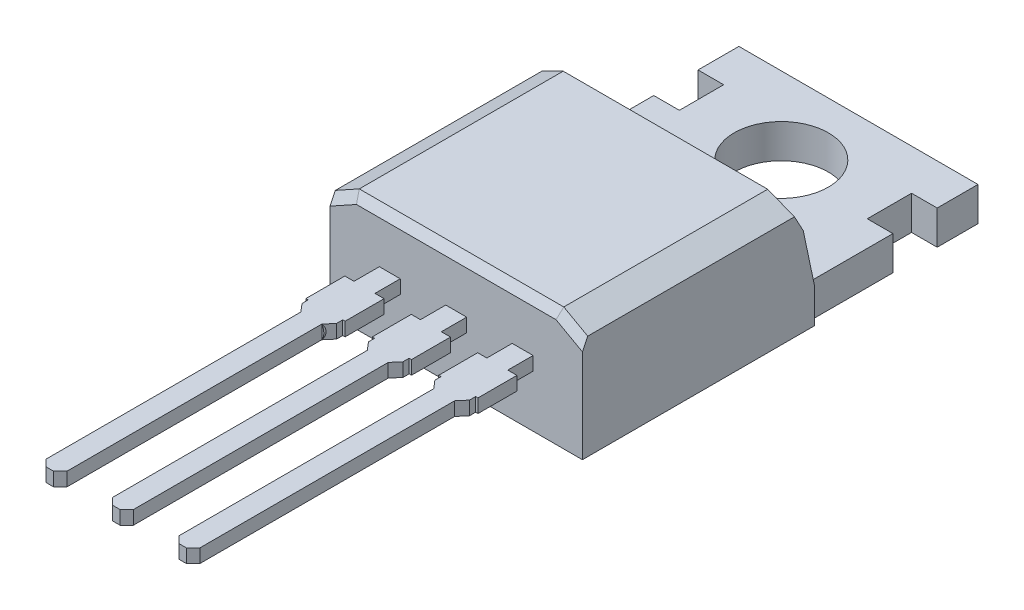
SolidWorks part; units mm, degrees
ref_plane "Front Plane" through (0, 0, 0) normal (0, 0, 1) x (1, 0, 0)
ref_plane "Top Plane" through (0, 0, 0) normal (0, 1, 0) x (1, 0, 0)
ref_plane "Right Plane" through (0, 0, 0) normal (1, 0, 0) x (0, 0, -1)
sketch "Sketch1" plane through (0, 0, 0) normal (0, 1, 0) x (1, 0, 0)
  line L0 (4.826, -1.0795) -> (-4.826, -1.0795)
  line L1 (4.826, -7.3025) -> (-4.826, -7.3025)
  line L2 (4.826, -7.3025) -> (4.826, 8.2138)
  line L3 (4.826, 7.3025) -> (-4.826, 7.3025)
  line L4 (-4.826, -7.3025) -> (-4.826, 8.2138)
  line L5 (4.826, -7.3025) -> (-4.826, 7.3025) construction
  line L6 (4.826, 7.3025) -> (-4.826, -7.3025) construction
  line L7 (4.826, -1.0795) -> (-4.826, -1.0795)
  line L8 (3.7898, 8.9789) -> (-3.7898, 8.9789)
  line L9 (-4.826, 8.2138) -> (-3.7898, 8.9789)
  line L10 (0, 7.3025) -> (0, 12.7866) construction
  line L11 (4.826, 8.2138) -> (3.7898, 8.9789)
  line L12 (4.826, 8.9789) -> (-4.826, 8.9789) construction
  point P0 (0, 0)
  dimension "D1" = 9.652
  dimension "D2" = 14.605
  dimension "D3" = 8.382
  dimension "D4" = 8.382
  dimension "D5" = 1.6764
sketch "Sketch2" plane through (0, 0, 0) normal (1, 0, 0) x (0, 0, -1)
  line L0 (14.3005, 0) -> (-1.0795, 0)
  line L1 (7.3025, 0) -> (12.7866, 0) construction
  line L2 (7.8005, 1.3) -> (7.124, 4.5)
  line L3 (7.124, 4.5) -> (-1.0795, 4.5)
  line L4 (-1.0795, 4.5) -> (-1.0795, 0)
  line L5 (14.3005, 1.3) -> (14.3005, 0)
  line L6 (14.3005, 1.3) -> (7.8005, 1.3)
  line L7 (14.3005, 1.3) -> (-7.3025, 1.3) construction
  line L8 (14.3005, 0) -> (-7.3025, 0) construction
  dimension "D1" = 4.5
  dimension "D3" = 6.5
  dimension "D2" = 15.38
extrude "Extrude1" add sketch "Sketch2" against normal up to vertex (4.826 mm away) and the other way up to vertex (4.826 mm away) up to point (-4.826, 0, 1.0795) other way up to point (4.826, 0, 1.0795)
sketch "Sketch10" plane through (0, 1.3, 0) normal (0, 1, 0) x (1, 0, 0)
  line L0 (0, 7.8005) -> (0, 16.6747) construction
  line L1 (-4.826, 7.8005) -> (4.826, 7.8005) construction
  line L2 (-4.826, 14.3005) -> (4.826, 14.3005) construction
  line L3 (-4.826, 14.3005) -> (-4.826, 7.8005) construction
  line L4 (-4.826, 12.7393) -> (-3.5922, 12.7393)
  line L5 (-4.826, 12.7393) -> (-4.826, 11.0462)
  line L6 (-4.826, 11.0462) -> (-3.5922, 11.0462)
  line L7 (-3.5922, 12.7393) -> (-3.5922, 11.0462)
  line L8 (3.5922, 12.7393) -> (3.5922, 11.0462)
  line L9 (4.826, 11.0462) -> (3.5922, 11.0462)
  line L10 (4.826, 12.7393) -> (4.826, 11.0462)
  line L11 (4.826, 12.7393) -> (3.5922, 12.7393)
  circle A0 centre (0, 11.3505) radius 1.8
  dimension "D1" = 3.6
  dimension "D2" = 2.95
extrude "Extrude5" cut sketch "Sketch10" against normal through all
sketch "Sketch6" plane through (0, 0, 1.0795) normal (0, 0, 1) x (1, 0, 0)
  line L0 (0, 4.5) -> (0, 0) construction
  line L1 (-4.826, 4.5) -> (4.826, 4.5) construction
  line L2 (-2.54, 4.5) -> (-2.54, 0) construction
  line L3 (2.54, 4.5) -> (2.54, 0) construction
  line L4 (-4.826, 2.25) -> (4.826, 2.25) construction
  line L5 (-4.826, 4.5) -> (-4.826, 0) construction
  line L6 (4.826, 4.5) -> (4.826, 0) construction
  line L7 (2.14, 2.51) -> (2.94, 2.51)
  line L8 (-2.94, 2.51) -> (-2.14, 2.51)
  line L9 (-2.94, 2.51) -> (-2.94, 1.99)
  line L10 (-2.94, 1.99) -> (-2.14, 1.99)
  line L11 (-2.14, 2.51) -> (-2.14, 1.99)
  line L12 (-2.94, 2.51) -> (-2.14, 1.99) construction
  line L13 (-2.94, 1.99) -> (-2.14, 2.51) construction
  line L14 (2.14, 2.51) -> (2.14, 1.99)
  line L15 (2.14, 1.99) -> (2.94, 1.99)
  line L16 (2.94, 2.51) -> (2.94, 1.99)
  line L17 (2.14, 2.51) -> (2.94, 1.99) construction
  line L18 (2.14, 1.99) -> (2.94, 2.51) construction
  line L19 (-0.4, 2.51) -> (0.4, 2.51)
  line L20 (-0.4, 2.51) -> (-0.4, 1.99)
  line L21 (-0.4, 1.99) -> (0.4, 1.99)
  line L22 (0.4, 2.51) -> (0.4, 1.99)
  line L23 (-0.4, 2.51) -> (0.4, 1.99) construction
  line L24 (-0.4, 1.99) -> (0.4, 2.51) construction
  point P15 (-2.54, 2.25)
  point P21 (2.54, 2.25)
  point P26 (0, 2.25)
  dimension "D3" = 0.8
  dimension "D4" = 0.52
  dimension "D5" = 0.8
  dimension "D6" = 0.8
  dimension "D1" = 2.54
  dimension "D2" = 2.54
extrude "Extrude6" add sketch "Sketch6" along normal blind 13
sketch "Sketch11" plane through (0, 2.51, 0) normal (0, 1, 0) x (1, 0, 0)
  line L0 (-2.94, -7.5795) -> (-2.14, -7.5795) construction
  line L1 (-2.94, -14.0795) -> (-2.94, -1.0795) construction
  line L2 (-2.14, -14.0795) -> (-2.14, -1.0795) construction
  line L3 (-2.54, -7.5795) -> (-2.54, 1.2721) construction
  line L4 (-4.826, -1.0795) -> (4.826, -1.0795) construction
  line L5 (-3.29, -2.0475) -> (-1.79, -2.0475)
  line L6 (-3.29, -2.0475) -> (-3.29, -3.5395)
  line L7 (-2.94, -4.0795) -> (-2.14, -4.0795)
  line L8 (-1.8796, -3.7747) -> (-1.8796, -3.5395)
  line L9 (-3.29, -2.0475) -> (-1.869, -4.1434) construction
  line L10 (-3.1272, -4.0199) -> (-1.79, -2.0475) construction
  line L11 (-3.29, -3.5395) -> (-3.2004, -3.5395)
  line L12 (-0.75, -2.0475) -> (0.75, -2.0475)
  line L13 (-2.14, -4.0795) -> (-1.8796, -3.7747)
  line L14 (-2.94, -4.0795) -> (-3.2004, -3.7747)
  line L15 (-3.2004, -3.7747) -> (-3.2004, -3.5395)
  line L16 (-1.79, -3.5395) -> (-1.8796, -3.5395)
  line L17 (-1.79, -2.0475) -> (-1.79, -3.5395)
  line L18 (-0.75, -2.0475) -> (-0.75, -3.5395)
  line L19 (-0.4, -4.0795) -> (0.4, -4.0795)
  line L20 (0.6604, -3.7747) -> (0.6604, -3.5395)
  line L21 (-0.75, -3.5395) -> (-0.6604, -3.5395)
  line L22 (0.4, -4.0795) -> (0.6604, -3.7747)
  line L23 (-0.4, -4.0795) -> (-0.6604, -3.7747)
  line L24 (-0.6604, -3.7747) -> (-0.6604, -3.5395)
  line L25 (0.75, -3.5395) -> (0.6604, -3.5395)
  line L26 (0.75, -2.0475) -> (0.75, -3.5395)
  line L27 (-0.75, -2.0475) -> (0.671, -4.1434) construction
  line L28 (-0.5872, -4.0199) -> (0.75, -2.0475) construction
  line L29 (1.79, -2.0475) -> (3.29, -2.0475)
  line L30 (1.79, -2.0475) -> (1.79, -3.5395)
  line L31 (2.14, -4.0795) -> (2.94, -4.0795)
  line L32 (3.2004, -3.7747) -> (3.2004, -3.5395)
  line L33 (1.79, -3.5395) -> (1.8796, -3.5395)
  line L34 (2.94, -4.0795) -> (3.2004, -3.7747)
  line L35 (2.14, -4.0795) -> (1.8796, -3.7747)
  line L36 (1.8796, -3.7747) -> (1.8796, -3.5395)
  line L37 (3.29, -3.5395) -> (3.2004, -3.5395)
  line L38 (3.29, -2.0475) -> (3.29, -3.5395)
  line L39 (1.79, -2.0475) -> (3.211, -4.1434) construction
  line L40 (1.9528, -4.0199) -> (3.29, -2.0475) construction
  point P8 (-2.54, -3.1537)
  point P15 (0, -3.1537)
  point P25 (-2.54, -4.0795)
  point P27 (-2.54, -2.0475)
  point P38 (0, -4.0795)
  point P40 (0, -2.0475)
  point P41 (2.54, -3.1537)
  point P53 (2.54, -4.0795)
  point P55 (2.54, -2.0475)
  dimension "D1" = 2.032
  dimension "D2" = 3
  dimension "D3" = 2.46
  dimension "D5" = 1.5
  dimension "D6" = 0.3048
  dimension "D4" = 1.3208
extrude "Extrude7" add sketch "Sketch11" against normal up to vertex
chamfer "Chamfer1" distance 0.254 angle 45 6 edges at (2.94, 2.25, 14.0795) (2.14, 2.25, 14.0795) (0.4, 2.25, 14.0795) (-0.4, 2.25, 14.0795) (-2.14, 2.25, 14.0795) (-2.94, 2.25, 14.0795)
sketch "Sketch12" plane through (-4.826, 0, 0) normal (-1, 0, 0) x (0, 0, 1)
  line L0 (1.0795, 0) -> (-11.0462, 0) construction
  line L1 (-15.1802, 2.7361) -> (-7.8005, 2.7361)
  line L2 (-15.1802, 2.7361) -> (-15.1802, 0)
  line L3 (-15.1802, 0) -> (-7.8005, 0)
  line L4 (-7.8005, 2.7361) -> (-7.8005, 0)
extrude "Extrude8" cut sketch "Sketch12" against normal blind 0.254
sketch "Sketch13" plane through (4.826, 0, 0) normal (1, 0, 0) x (0, 0, -1)
  line L4 (15.1802, 2.7361) -> (7.8005, 2.7361)
  line L5 (7.8005, 2.7361) -> (7.8005, 0)
  line L6 (7.8005, 0) -> (15.1802, 0)
  line L7 (15.1802, 0) -> (15.1802, 2.7361)
  line L8 (15.1802, 2.7361) -> (7.8005, 2.7361)
  line L9 (7.8005, 2.7361) -> (7.8005, 0)
  line L10 (7.8005, 0) -> (15.1802, 0)
  line L11 (15.1802, 0) -> (15.1802, 2.7361)
  dimension "D1" = 0
extrude "Extrude9" cut sketch "Sketch13" against normal blind 0.254
chamfer "Chamfer2" distance 0.508 angle 61 2 edges at (4.826, 4.5, -3.0223) (-4.826, 4.5, -3.0223)
chamfer "Chamfer3" distance 0.2032 angle 61 6 edges at (4.3678, 4.246, 1.0795) (0, 4.5, 1.0795) (-4.3678, 4.246, 1.0795) (4.3678, 4.246, -7.1777) (0, 4.5, -7.124) (-4.3678, 4.246, -7.1777)
ref_plane "Plane1" through (0, 0, 4.0795) normal (0, 0, 1) x (1, 0, 0)
sketch "Sketch15" plane through (0, 0, 4.0795) normal (0, 0, 1) x (1, 0, 0)
  line L0 (-2.14, 2.51) -> (-2.94, 2.51) construction
  line L1 (-2.14, 2.51) -> (-2.94, 2.51)
  line L2 (-2.94, 1.99) -> (-2.14, 1.99) construction
  line L3 (-2.94, 1.99) -> (-2.14, 1.99)
  arc A0 (-2.14, 1.99) -> (-2.14, 2.51) centre (-2.54, 2.25) ccw
  arc A1 (-2.94, 2.51) -> (-2.94, 1.99) centre (-2.54, 2.25) ccw
extrude "Extrude10" add sketch "Sketch15" against normal blind 1.016
